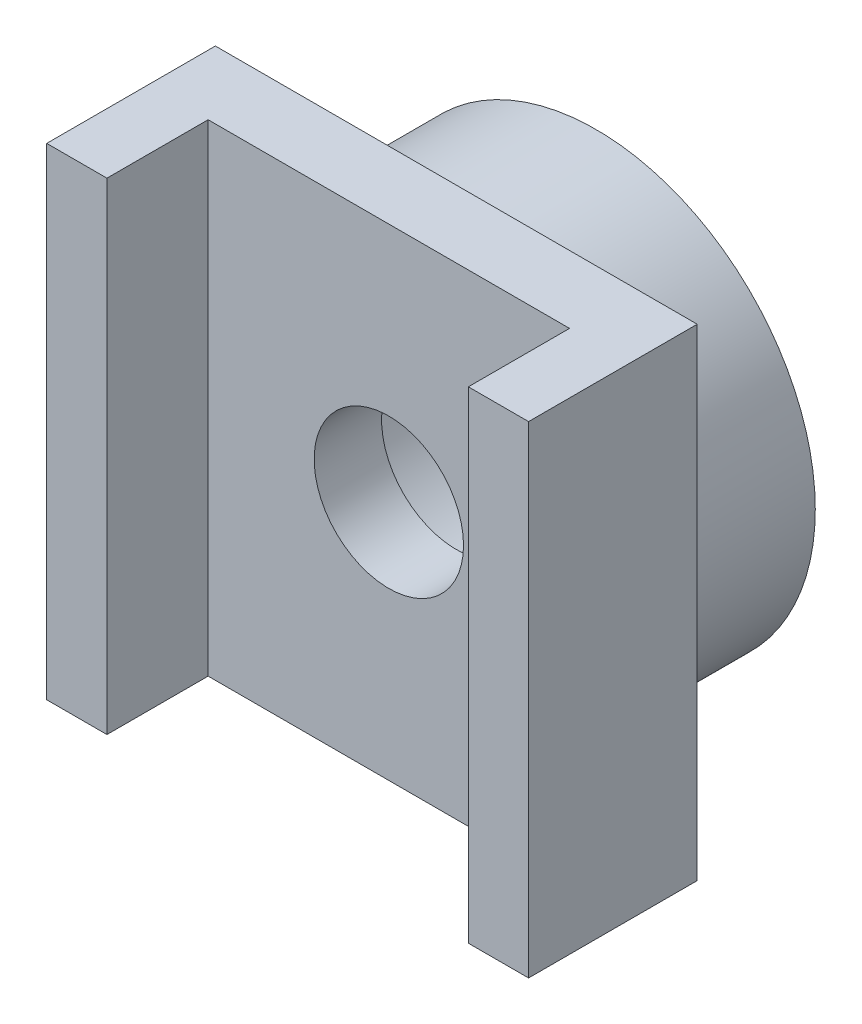
SolidWorks part; units mm, degrees
material "ПК/АБС"
ref_plane "Спереди" through (0, 0, 0) normal (0, 0, 1) x (1, 0, 0)
ref_plane "Сверху" through (0, 0, 0) normal (0, 1, 0) x (1, 0, 0)
ref_plane "Справа" through (0, 0, 0) normal (1, 0, 0) x (0, 0, -1)
sketch "Эскиз1" plane through (0, 0, 0) normal (0, 0, 1) x (1, 0, 0)
  circle A0 centre (0, 0) radius 4.55
  circle A1 centre (0, 0) radius 2.8
  dimension "D1" = 9.1
  dimension "D2" = 5.6
extrude "Вытянуть1" add sketch "Эскиз1" along normal blind 2.9
sketch "Эскиз2" plane through (0, 0, 2.9) normal (0, 0, 1) x (1, 0, 0)
  line L0 (-5, 5) -> (5, -5) construction
  line L1 (-5, -5) -> (5, -5)
  line L2 (-5, -5) -> (-5, 5)
  line L3 (-5, 5) -> (5, 5)
  line L4 (5, -5) -> (5, 5)
  line L5 (5, 5) -> (-5, -5) construction
  circle A0 centre (0, 0) radius 1.55
  circle M1 centre (0, 0) radius 4.55
  circle M2 centre (0, 0) radius 2.8
  dimension "D3" = 3.1
  dimension "D1" = 10
  dimension "D2" = 10
extrude "Вытянуть2" add sketch "Эскиз2" along normal blind 1.4 contours L1 L4 L3 L2 M1 | M2 | M1 M2
sketch "Эскиз3" plane through (0, 0, 4.3) normal (0, 0, 1) x (1, 0, 0)
  line L0 (-3.75, 5) -> (-3.75, -5)
  line L1 (-5, 5) -> (5, 5) construction
  line L2 (-5, -5) -> (5, -5) construction
  line L3 (3.75, 5) -> (3.75, -5)
  line L4 (-5, -5) -> (-5, 5) construction
  line M1 (-5, -5) -> (5, -5)
  line M2 (5, -5) -> (5, 5)
  line M3 (5, 5) -> (-5, 5)
  line M4 (-5, 5) -> (-5, -5)
  dimension "D1" = 7.5
  dimension "D2" = 1.25
extrude "Вытянуть3" add sketch "Эскиз3" along normal blind 2.1 contours L0 M1 M3 M4 | L3 M1 M2 M3
